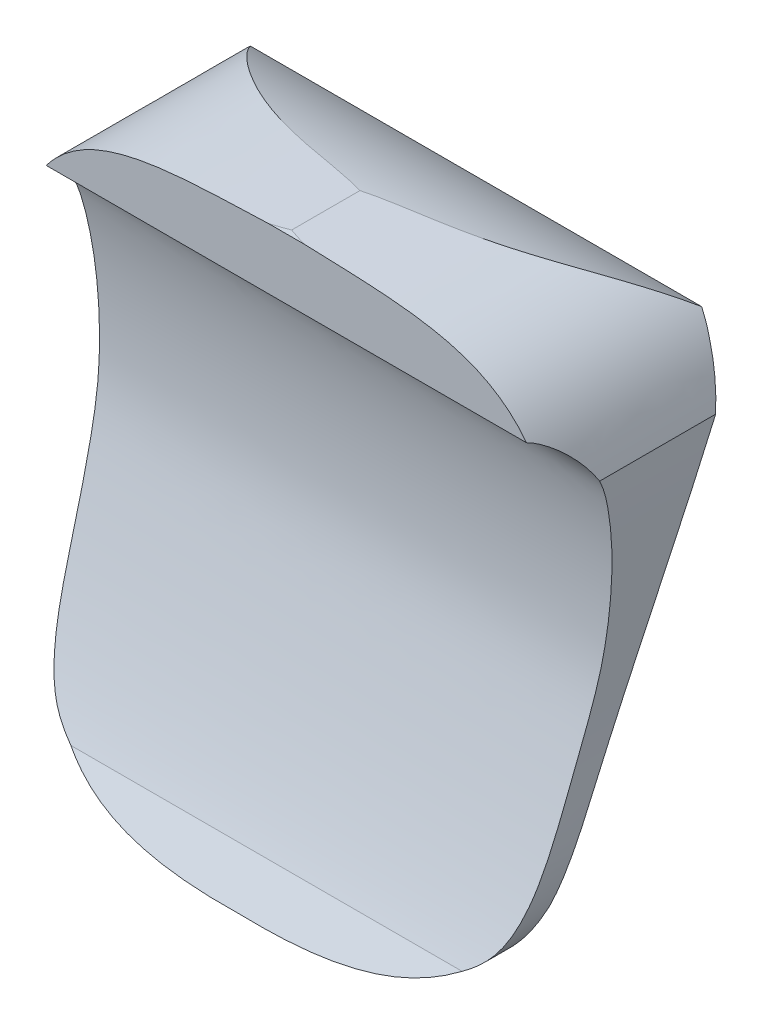
SolidWorks part; units mm, degrees
ref_plane "Front Plane" through (0, 0, 0) normal (0, 0, 1) x (1, 0, 0)
ref_plane "Top Plane" through (0, 0, 0) normal (0, 1, 0) x (1, 0, 0)
ref_plane "Right Plane" through (0, 0, 0) normal (1, 0, 0) x (0, 0, -1)
sketch "Sketch1" plane through (0, 0, 0) normal (0, 0, 1) x (1, 0, 0)
  line L0 (0, 54.4388) -> (-81.7228, 54.4388) construction
ref_plane "Plane2" through (0, 6.3681, 17.4963) normal (0, 0.342, 0.9397) x (-1, 0, 0)
sketch "Sketch2" plane through (0, 6.3681, 17.4963) normal (0, 0.342, 0.9397) x (-1, 0, 0)
  line L1 (-110, 110) -> (110, 110)
  line L2 (-110, 110) -> (-110, -110)
  line L3 (-110, -110) -> (110, -110)
  line L4 (110, 110) -> (110, -110)
  line L5 (-110, 110) -> (110, -110) construction
  line L6 (-110, -110) -> (110, 110) construction
  point P0 (0, 0)
  dimension "D1" = 220
  dimension "D2" = 220
extrude "Boss-Extrude1" add sketch "Sketch2" along normal blind 4
sketch "Sketch4" plane through (0, 0, 0) normal (1, 0, 0) x (0, 0, -1)
  line L1 (-73.1539, -124.7386) -> (-58.8773, -95.63)
  line L2 (-58.8773, -95.63) -> (16.3672, 111.1024)
  line L5 (-73.4914, 111.8306) -> (-73.4914, 141.8306)
  line L7 (16.3672, 111.1024) -> (20.0449, 119.6439)
  line L8 (-73.1539, -124.7386) -> (-116.6243, -218.9246)
  line L9 (-116.6243, -218.9246) -> (-141.6305, -207.3833)
  line L10 (-141.6305, -207.3833) -> (-83.2872, -120.0617)
  spline S0 degree 3 poles (-83.2872, -120.0617) (-70.7029, -92.7957) (-48.7703, -25.9021) (-38.7105, 12.5493) (-39.6234, 59.8101) (-50.0435, 96.0471) (-64.9002, 108.7906) (-73.4914, 111.8306) knots 0 0 0 0 0.291321 0.538048 0.793152 0.839348 1 1 1 1
  spline S1 degree 2 poles (-73.4914, 141.8306) (-21.8387, 148.9004) (20.0449, 119.6439) knots 0 0 0 1 1 1
  point P0 (-83.2872, -120.0617)
  point P1 (-51.3816, -32.3215)
  point P2 (-40.5574, 16.7235)
  point P3 (-46.3798, 82.8247)
  point P4 (-73.4914, 111.8306)
  dimension "D1" = 30
extrude "Boss-Extrude2" add sketch "Sketch4" along normal blind 130 and the other way blind 130
sketch "Sketch6" plane through (0, 0, 0) normal (0, 0, 1) x (1, 0, 0)
  line L0 (130, -95.63) -> (130, 111.1024) construction
  line L1 (0, 142.1661) -> (0, 0) construction
  line L3 (-135.6267, 225.5684) -> (135.6267, 225.5684)
  line L4 (-135.6267, 225.5684) -> (-135.6267, -225.5684)
  line L5 (-135.6267, -225.5684) -> (135.6267, -225.5684)
  line L6 (135.6267, 225.5684) -> (135.6267, -225.5684)
  line L7 (-135.6267, 225.5684) -> (135.6267, -225.5684) construction
  line L8 (-135.6267, -225.5684) -> (135.6267, 225.5684) construction
  spline S0 degree 3 poles (0, 142.1661) (64.7299, 139.5109) (112.5303, 142.6951) (130, 88.9284) knots 0 0 0 0 1 1 1 1
  spline S1 degree 3 poles (130, 88.9284) (127.7908, 44.5636) (121.3204, -17.1562) (118.6055, -103.0083) (79.5086, -134.2768) (41.1137, -138.8723) (0, -138.3177) knots 0 0 0 0 0.431824 0.636023 0.692841 1 1 1 1
  spline S2 degree 3 poles (-130, 88.9284) (-127.7908, 44.5636) (-121.3204, -17.1562) (-118.6055, -103.0083) (-79.5086, -134.2768) (-41.1137, -138.8723) (0, -138.3177) knots 0 0 0 0 0.431824 0.636023 0.692841 1 1 1 1
  spline S3 degree 3 poles (0, 142.1661) (-64.7299, 139.5109) (-112.5303, 142.6951) (-130, 88.9284) knots 0 0 0 0 1 1 1 1
  point P0 (0, 142.1661)
  point P1 (106.0502, 123.9272)
  point P2 (130, 88.9284)
  point P3 (120.8385, -47.1235)
  point P6 (103.5855, -114.6565)
  point P7 (0, -138.3177)
extrude "Cut-Extrude3" cut sketch "Sketch6" against normal through all and the other way through all
ref_plane "Plane3" through (0, 8.0782, 22.1948) normal (0, 0.342, 0.9397) x (-1, 0, 0)
sketch "Sketch7" plane through (0, 8.0782, 22.1948) normal (0, 0.342, 0.9397) x (-1, 0, 0)
  line L1 (-84.4872, -73.8421) -> (84.4872, -73.8421)
  line L2 (-84.4872, -73.8421) -> (-84.4872, 73.8421)
  line L3 (-84.4872, 73.8421) -> (84.4872, 73.8421)
  line L4 (84.4872, -73.8421) -> (84.4872, 73.8421)
  line L5 (-84.4872, -73.8421) -> (84.4872, 73.8421) construction
  line L6 (-84.4872, 73.8421) -> (84.4872, -73.8421) construction
  point P0 (0, 0)
